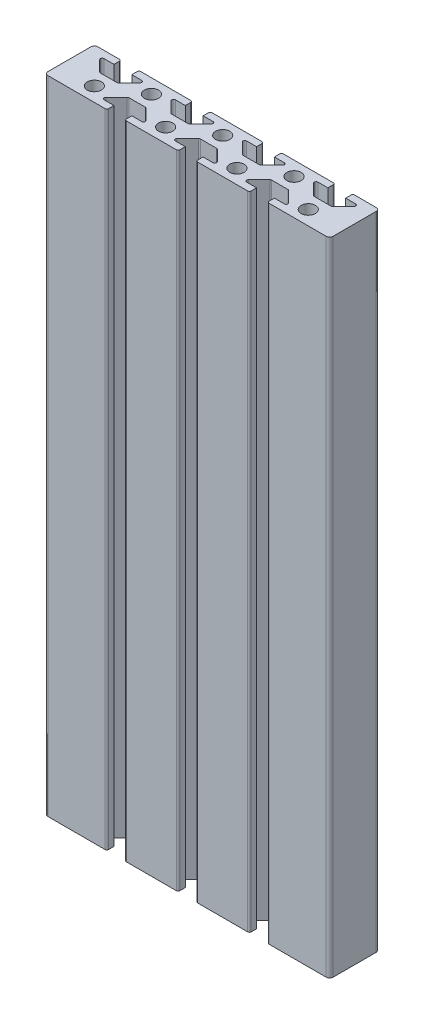
SolidWorks part; units mm, degrees
ref_plane "Front Plane" through (0, 0, 0) normal (0, 0, 1) x (1, 0, 0)
ref_plane "Top Plane" through (0, 0, 0) normal (0, 1, 0) x (1, 0, 0)
ref_plane "Right Plane" through (0, 0, 0) normal (1, 0, 0) x (0, 0, -1)
sketch "Sketch1" plane through (0, 0, 0) normal (0, 1, 0) x (1, 0, 0)
  line L0 (63.5, 12) -> (67.5, 12)
  line L1 (0, 0) -> (80, 0)
  line L2 (0, 0) -> (0, 14)
  line L3 (0, 14) -> (80, 14)
  line L4 (80, 0) -> (80, 14)
  line L5 (67.5, 12) -> (67.5, 14)
  line L6 (67.5, 14) -> (72.5, 14)
  line L7 (72.5, 14) -> (72.5, 12)
  line L9 (76.5, 12) -> (72.5, 8)
  line L10 (72.5, 8) -> (67.5, 8)
  line L11 (67.5, 8) -> (63.5, 12)
  line L12 (72.5, 12) -> (76.5, 12)
  line L13 (52.5, 12) -> (56.5, 12)
  line L14 (56.5, 12) -> (52.5, 8)
  line L15 (52.5, 8) -> (47.5, 8)
  line L16 (47.5, 8) -> (43.5, 12)
  line L17 (43.5, 12) -> (47.5, 12)
  line L18 (47.5, 12) -> (47.5, 14)
  line L19 (47.5, 14) -> (52.5, 14)
  line L20 (52.5, 14) -> (52.5, 12)
  line L21 (32.5, 12) -> (36.5, 12)
  line L22 (36.5, 12) -> (32.5, 8)
  line L23 (32.5, 8) -> (27.5, 8)
  line L24 (27.5, 8) -> (23.5, 12)
  line L25 (23.5, 12) -> (27.5, 12)
  line L26 (27.5, 12) -> (27.5, 14)
  line L27 (27.5, 14) -> (32.5, 14)
  line L28 (32.5, 14) -> (32.5, 12)
  line L29 (12.5, 12) -> (16.5, 12)
  line L30 (16.5, 12) -> (12.5, 8)
  line L31 (12.5, 8) -> (7.5, 8)
  line L32 (7.5, 8) -> (3.5, 12)
  line L33 (3.5, 12) -> (7.5, 12)
  line L34 (7.5, 12) -> (7.5, 14)
  line L35 (7.5, 14) -> (12.5, 14)
  line L36 (12.5, 14) -> (12.5, 12)
  line L37 (57.5, 0) -> (57.5, 2)
  line L38 (57.5, 2) -> (53.5, 2)
  line L39 (53.5, 2) -> (57.5, 6)
  line L40 (57.5, 6) -> (62.5, 6)
  line L41 (62.5, 6) -> (66.5, 2)
  line L42 (66.5, 2) -> (62.5, 2)
  line L43 (62.5, 2) -> (62.5, 0)
  line L44 (62.5, 0) -> (57.5, 0)
  line L45 (42.5, 0) -> (37.5, 0)
  line L46 (37.5, 0) -> (37.5, 2)
  line L47 (37.5, 2) -> (33.5, 2)
  line L48 (33.5, 2) -> (37.5, 6)
  line L49 (37.5, 6) -> (42.5, 6)
  line L50 (42.5, 6) -> (46.5, 2)
  line L51 (46.5, 2) -> (42.5, 2)
  line L52 (42.5, 2) -> (42.5, 0)
  line L53 (22.5, 0) -> (17.5, 0)
  line L54 (17.5, 0) -> (17.5, 2)
  line L55 (17.5, 2) -> (13.5, 2)
  line L56 (13.5, 2) -> (17.5, 6)
  line L57 (17.5, 6) -> (22.5, 6)
  line L58 (22.5, 6) -> (26.5, 2)
  line L59 (26.5, 2) -> (22.5, 2)
  line L60 (22.5, 2) -> (22.5, 0)
  circle A0 centre (60, 10) radius 2
  circle A1 centre (40, 10) radius 2
  circle A2 centre (20, 10) radius 2
  circle A3 centre (70, 4) radius 2
  circle A4 centre (50, 4) radius 2
  circle A5 centre (30, 4) radius 2
  circle A6 centre (10, 4) radius 2
  dimension "D17" = 4
  dimension "D21" = 4
  dimension "D1" = 80
  dimension "D2" = 14
  dimension "D3" = 7.5
  dimension "D4" = 5
  dimension "D5" = 6
  dimension "D6" = 17.5
  dimension "D7" = 2
  dimension "D8" = 4
  dimension "D9" = 5
  dimension "D10" = 5
  dimension "D11" = 4
  dimension "D12" = 4
  dimension "D13" = 2
  dimension "D14" = 2
  dimension "D15" = 6
  dimension "D16" = 3
  dimension "D18" = 20
  dimension "D19" = 4
  dimension "D22" = 10
  dimension "D23" = 4
  dimension "D20" = 3
  dimension "D24" = 4
extrude "Boss-Extrude1" add sketch "Sketch1" along normal blind 180 contours L59 L60 L1 L46 L47 L48 L49 L50 L51 L52 L37 L38 L39 L40 L41 L42 L43 L4 L3 L7 L12 L9 L10 L11 L0 L5 L20 L13 L14 L15 L16 L17 L18 L28 L21 L22 L23 L24 L25 L26 L36 L29 L30 L31 L32 L33
fillet "Fillet1" radius 0.5 24 edges at (67.5, 90, -8) (63.5, 90, -12) (76.5, 90, -12) (72.5, 90, -8) (47.5, 90, -8) (27.5, 90, -8) (52.5, 90, -8) (32.5, 90, -8) (56.5, 90, -12) (36.5, 90, -12) (43.5, 90, -12) (23.5, 90, -12) (12.5, 90, -8) (7.5, 90, -8) (3.5, 90, -12) (16.5, 90, -12) (72.5, 90, -14) (67.5, 90, -14) (52.5, 90, -14) (47.5, 90, -14) (32.5, 90, -14) (27.5, 90, -14) (12.5, 90, -14) (7.5, 90, -14)
fillet "Fillet2" radius 0.5 18 edges at (17.5, 90, -6) (26.5, 90, -2) (22.5, 90, -6) (22.5, 90, 0) (17.5, 90, 0) (13.5, 90, -2) (33.5, 90, -2) (37.5, 90, -6) (42.5, 90, -6) (42.5, 90, 0) (46.5, 90, -2) (37.5, 90, 0) (57.5, 90, 0) (62.5, 90, 0) (53.5, 90, -2) (57.5, 90, -6) (66.5, 90, -2) (62.5, 90, -6)
fillet "Fillet3" radius 1 4 edges at (0, 90, -14) (0, 90, 0) (80, 90, -14) (80, 90, 0)
sketch "Sketch2" plane through (0, 0, -14) normal (0, 0, -1) x (-1, 0, 0)
  line L0 (-33, 0) -> (-47, 0) construction
  circle A1 centre (-40, 10) radius 2.5
  dimension "D1" = 10
  dimension "D2" = 5
extrude "Cut-Extrude2" cut sketch "Sketch2" against normal blind 230 contours A1
sketch "Sketch3" plane through (0, 0, -14) normal (0, 0, -1) x (-1, 0, 0)
  circle A0 centre (-40, 10) radius 5.5
  dimension "D1" = 11
extrude "Cut-Extrude3" cut sketch "Sketch3" against normal blind 7 contours A0
sketch "Sketch4" plane through (0, 0, -14) normal (0, 0, -1) x (-1, 0, 0)
  line L0 (-33, 180) -> (-47, 180) construction
  circle A0 centre (-40, 170) radius 2.5
  dimension "D1" = 5
  dimension "D2" = 10
extrude "Cut-Extrude4" cut sketch "Sketch4" against normal blind 7
sketch "Sketch5" plane through (0, 0, -14) normal (0, 0, -1) x (-1, 0, 0)
  circle A0 centre (-40, 170) radius 5.5
  dimension "D1" = 11
extrude "Cut-Extrude5" cut sketch "Sketch5" against normal blind 7
